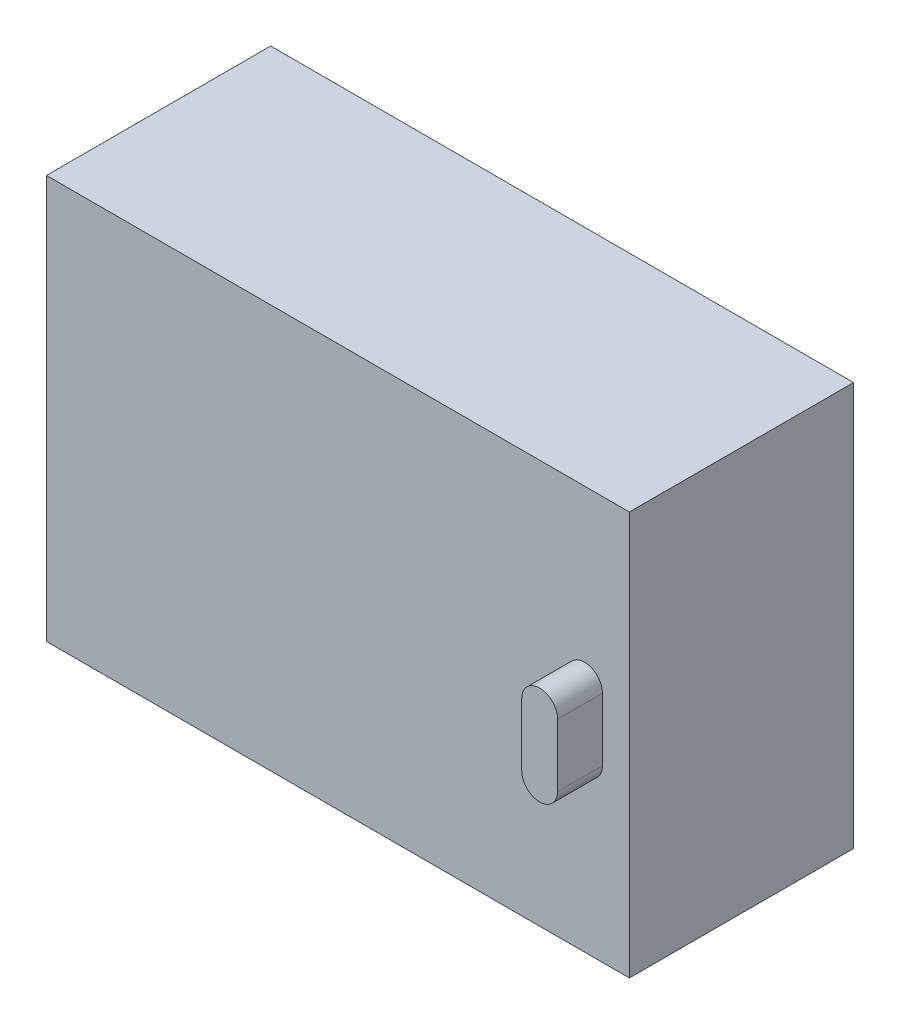
SolidWorks part; units mm, degrees
ref_plane "Front" through (0, 0, 0) normal (0, 0, 1) x (1, 0, 0)
ref_plane "Top" through (0, 0, 0) normal (0, 1, 0) x (1, 0, 0)
ref_plane "Right" through (0, 0, 0) normal (1, 0, 0) x (0, 0, -1)
sketch "Эскиз1" plane through (0, 0, 0) normal (1, 0, 0) x (0, 0, -1)
  line L0 (0, 0) -> (0, 90)
  line L1 (0, 90) -> (50, 90)
  line L2 (50, 90) -> (50, 0)
  line L3 (50, 0) -> (0, 0)
  dimension "D1" = 90
  dimension "D2" = 50
extrude "Бобышка-Вытянуть1" add sketch "Эскиз1" against normal blind 130
sketch "Эскиз2" plane through (0, 0, 0) normal (0, 0, 1) x (1, 0, 0)
  line L0 (-130, 45) -> (0, 45) construction
  line L1 (-130, 90) -> (-130, 0) construction
  line L2 (0, 90) -> (0, 0) construction
  line L3 (-10, 38) -> (-10, 52) construction
  line L4 (-14, 38) -> (-14, 52)
  line L5 (-6, 38) -> (-6, 52)
  arc A0 (-14, 38) -> (-6, 38) centre (-10, 38) ccw
  arc A1 (-6, 52) -> (-14, 52) centre (-10, 52) ccw
  point P8 (-10, 45)
  dimension "D1" = 8
  dimension "D2" = 14
  dimension "D3" = 10
extrude "Бобышка-Вытянуть2" add sketch "Эскиз2" along normal blind 10
